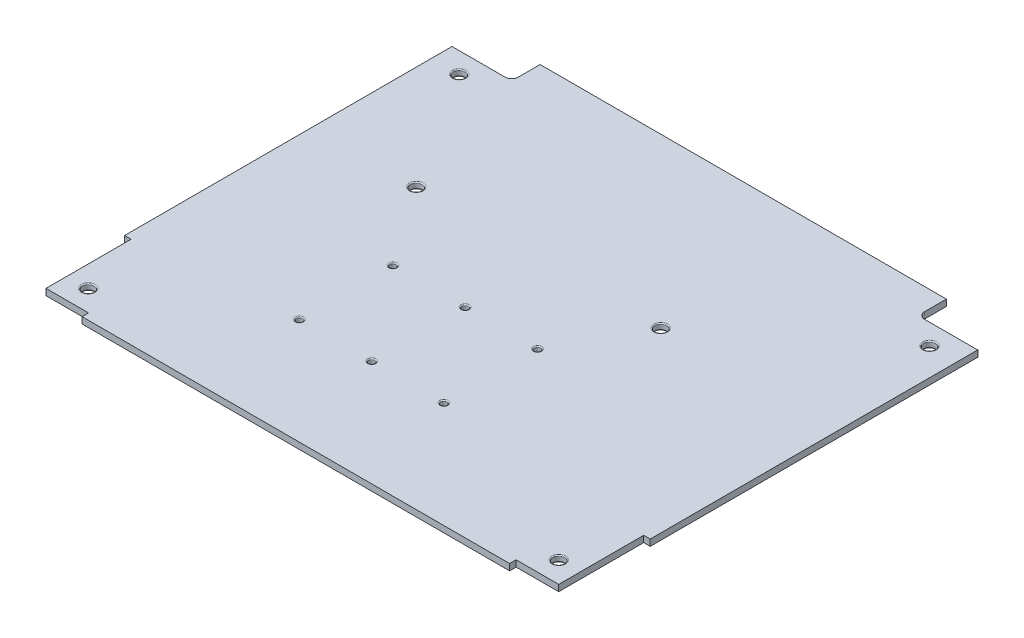
SolidWorks part; units mm, degrees
ref_plane "Front Plane" through (0, 0, 0) normal (0, 0, 1) x (1, 0, 0)
ref_plane "Top Plane" through (0, 0, 0) normal (0, 1, 0) x (1, 0, 0)
ref_plane "Right Plane" through (0, 0, 0) normal (1, 0, 0) x (0, 0, -1)
sketch "Sketch1" plane through (0, 0, 0) normal (0, 1, 0) x (1, 0, 0)
  line L1 (-123.65, -105.2375) -> (123.65, -105.2375)
  line L2 (-123.65, -105.2375) -> (-123.65, 105.2375)
  line L3 (-123.65, 105.2375) -> (123.65, 105.2375)
  line L4 (123.65, -105.2375) -> (123.65, 105.2375)
  line L5 (-123.65, -105.2375) -> (123.65, 105.2375) construction
  line L6 (-123.65, 105.2375) -> (123.65, -105.2375) construction
  point P0 (0, 0)
  dimension "D1" = 247.3
  dimension "D2" = 210.475
extrude "Boss-Extrude1" add sketch "Sketch1" along normal blind 3
sketch "Sketch4" plane through (0, 3, 0) normal (0, 1, 0) x (1, 0, 0)
  line L0 (0, 0) -> (0, -50000) construction
  line L5 (120.6, -102.1875) -> (100.6, -105.2375) construction
  line L15 (-123.65, -105.2375) -> (-120.6, -105.2375)
  line L16 (-123.65, -105.2375) -> (-123.65, -62.1875)
  line L21 (-123.65, -62.1875) -> (-120.6, -62.1875)
  line L23 (-120.6, -102.1875) -> (-120.6, -62.1875)
  line L24 (-123.65, -105.2375) -> (-120.6, -62.1875) construction
  line L25 (-123.65, -62.1875) -> (-120.6, -105.2375) construction
  line L34 (0, 0) -> (50000, 0) construction
  line L35 (-120.6, -105.2375) -> (-100.6, -105.2375)
  line L37 (-120.6, -102.1875) -> (-100.6, -102.1875)
  line L38 (-100.6, -105.2375) -> (-100.6, -102.1875)
  line L39 (-120.6, -105.2375) -> (-100.6, -102.1875) construction
  line L40 (-120.6, -102.1875) -> (-100.6, -105.2375) construction
  line L41 (120.6, -105.2375) -> (100.6, -102.1875) construction
  line L42 (123.65, -62.1875) -> (120.6, -105.2375) construction
  line L43 (123.65, -105.2375) -> (120.6, -62.1875) construction
  line L44 (100.6, -105.2375) -> (100.6, -102.1875)
  line L45 (120.6, -102.1875) -> (100.6, -102.1875)
  line L46 (120.6, -105.2375) -> (100.6, -105.2375)
  line L47 (120.6, -102.1875) -> (120.6, -62.1875)
  line L48 (123.65, -62.1875) -> (120.6, -62.1875)
  line L49 (123.65, -105.2375) -> (123.65, -62.1875)
  line L50 (123.65, -105.2375) -> (120.6, -105.2375)
  point P4 (-122.125, -83.7125)
  point P9 (-110.6, -103.7125)
  point P19 (110.6, -103.7125)
  point P20 (122.125, -83.7125)
  dimension "D1" = 43.05
  dimension "D2" = 3.05
  dimension "D3" = 3.05
  dimension "D4" = 23.05
extrude "Cut-Extrude2" cut sketch "Sketch4" against normal through all
sketch "Sketch2" plane through (0, 3, 0) normal (0, 1, 0) x (1, 0, 0)
  line L0 (0, 0) -> (50000, 0) construction
  line L1 (0, 0) -> (0, 50000) construction
  line L2 (-123.65, 105.2375) -> (-123.65, -62.1875) construction
  line L3 (123.65, 105.2375) -> (-123.65, 105.2375) construction
  line L4 (-100.6, -105.2375) -> (100.6, -105.2375) construction
  circle A0 centre (-110.65, 82.2375) radius 2.75
  circle A1 centre (110.65, 82.2375) radius 2.75
  circle A4 centre (-110.65, -92.2375) radius 2.75
  circle A5 centre (110.65, -92.2375) radius 2.75
  dimension "D1" = 5.5
  dimension "D2" = 13
  dimension "D3" = 23
  dimension "D4" = 13
extrude "Cut-Extrude1" cut sketch "Sketch2" against normal through all
fillet "Fillet1" radius 0.5 8 edges at (-110.65, 3, -79.4875) (-110.65, 0, -79.4875) (110.65, 3, -84.9875) (110.65, 0, -84.9875) (-110.65, 3, 94.9875) (-110.65, 0, 94.9875) (110.65, 3, 89.4875) (110.65, 0, 89.4875)
sketch "Sketch5" plane through (0, 3, 0) normal (0, 1, 0) x (1, 0, 0)
  line L5 (-10, 35.175) -> (10, 35.175)
  line L6 (15.05, 40.225) -> (15.05, 105.2375)
  line L8 (-15.05, 105.2375) -> (-15.05, 40.225)
  line L9 (-10, 35.225) -> (10, 35.225)
  line L10 (15, 40.225) -> (15, 92.225)
  line L11 (15, 92.225) -> (-15, 92.225)
  line L12 (-15, 92.225) -> (-15, 40.225)
  line L13 (-10, 35.225) -> (10, 35.225) construction
  line L14 (15, 40.225) -> (15, 92.225) construction
  line L15 (15, 92.225) -> (-15, 92.225) construction
  line L16 (-15, 92.225) -> (-15, 40.225) construction
  line L17 (15.05, 92.275) -> (-15.05, 92.275) construction
  line L18 (-15.05, 105.2375) -> (15.05, 105.2375)
  line L19 (123.65, 105.2375) -> (-123.65, 105.2375) construction
  line L20 (15.05, 40.225) -> (15.05, 92.275) construction
  line L21 (-15.05, 92.275) -> (-15.05, 40.225) construction
  arc A2 (10, 35.175) -> (15.05, 40.225) centre (10, 40.225) ccw
  arc A3 (-15.05, 40.225) -> (-10, 35.175) centre (-10, 40.225) ccw
  arc A4 (10, 35.225) -> (15, 40.225) centre (10, 40.225) ccw
  arc A5 (-15, 40.225) -> (-10, 35.225) centre (-10, 40.225) ccw
  arc A6 (10, 35.225) -> (15, 40.225) centre (10, 40.225) ccw construction
  arc A7 (-15, 40.225) -> (-10, 35.225) centre (-10, 40.225) ccw construction
  dimension "D1" = 0
  dimension "D2" = 0.05
extrude "Cut-Extrude3" [suppressed] cut sketch "Sketch5" against normal through all
sketch "Sketch6" plane through (0, 3, 0) normal (0, 1, 0) x (1, 0, 0)
  line L0 (-123.65, 105.2375) -> (-123.65, -62.1875) construction
  line L1 (-123.65, -72.4875) -> (-98.57, -72.4875)
  line L2 (-123.65, -72.4875) -> (-123.65, -8.8875)
  line L3 (-123.65, -8.8875) -> (-98.57, -8.8875)
  line L4 (-95.57, -69.4875) -> (-95.57, -11.8875)
  line L5 (-100.6, -105.2375) -> (100.6, -105.2375) construction
  line L6 (0, 0) -> (0, -50000) construction
  line L7 (95.57, -69.4875) -> (95.57, -11.8875)
  line L8 (123.65, -8.8875) -> (98.57, -8.8875)
  line L9 (123.65, -72.4875) -> (123.65, -8.8875)
  line L10 (123.65, -72.4875) -> (98.57, -72.4875)
  arc A0 (98.57, -72.4875) -> (95.57, -69.4875) centre (98.57, -69.4875) cw
  arc A1 (95.57, -11.8875) -> (98.57, -8.8875) centre (98.57, -11.8875) cw
  arc A2 (-98.57, -72.4875) -> (-95.57, -69.4875) centre (-98.57, -69.4875) ccw
  arc A3 (-95.57, -11.8875) -> (-98.57, -8.8875) centre (-98.57, -11.8875) ccw
  point P17 (95.57, -72.4875)
  point P20 (95.57, -8.8875)
  point P23 (-95.57, -72.4875)
  point P26 (-95.57, -8.8875)
  dimension "D4" = 3
  dimension "D1" = 32.75
  dimension "D2" = 63.6
  dimension "D3" = 28.08
extrude "Cut-Extrude4" [suppressed] cut sketch "Sketch6" against normal through all
sketch "Sketch8" plane through (0, 3, 0) normal (0, 1, 0) x (1, 0, 0)
  line L0 (-14.35, -33.2375) -> (-14.35, 49966.7625) construction
  line L1 (53.65, -55.2375) -> (-82.35, -55.2375) construction
  line L2 (53.65, -55.2375) -> (53.65, -11.2375) construction
  line L3 (53.65, -11.2375) -> (-82.35, -11.2375) construction
  line L4 (-82.35, -55.2375) -> (-82.35, -11.2375) construction
  line L5 (53.65, -55.2375) -> (-82.35, -11.2375) construction
  line L6 (53.65, -11.2375) -> (-82.35, -55.2375) construction
  line L7 (-14.35, -33.2375) -> (-50014.35, -33.2375) construction
  circle A0 centre (19.65, -55.2375) radius 1.5
  circle A1 centre (-14.35, -55.2375) radius 1.5
  circle A2 centre (-48.35, -55.2375) radius 1.5
  circle A3 centre (-48.35, -11.2375) radius 1.5
  circle A4 centre (-14.35, -11.2375) radius 1.5
  circle A5 centre (19.65, -11.2375) radius 1.5
  point P4 (-14.35, -33.2375)
  dimension "D1" = 3
  dimension "D3" = 34
extrude "Cut-Extrude6" cut sketch "Sketch8" against normal through all
fillet "Fillet2" radius 0.5 12 edges at (19.65, 3, 56.7375) (19.65, 0, 56.7375) (-14.35, 3, 56.7375) (-14.35, 0, 56.7375) (-48.35, 3, 53.7375) (-48.35, 0, 53.7375) (-48.35, 3, 12.7375) (-48.35, 0, 12.7375) (-14.35, 3, 9.7375) (-14.35, 0, 9.7375) (19.65, 3, 9.7375) (19.65, 0, 9.7375)
sketch "Sketch9" plane through (0, 3, 0) normal (0, 1, 0) x (1, 0, 0)
  circle A2 centre (-74.85, 26.2625) radius 2.75 construction
  circle A5 centre (40.15, 26.2625) radius 2.75 construction
  circle A8 centre (-74.85, 26.2625) radius 2.75
  circle A11 centre (40.15, 26.2625) radius 2.75
extrude "Cut-Extrude7" cut sketch "Sketch9" against normal through all
fillet "Fillet3" radius 0.5 4 edges at (-74.85, 3, -23.5125) (-74.85, 0, -23.5125) (40.15, 3, -23.5125) (40.15, 0, -23.5125)
sketch "Sketch10" [suppressed] plane through (0, 3, 0) normal (0, 1, 0) x (1, 0, 0)
  circle A0 centre (74.85, 49.2625) radius 2.75 construction
  circle A1 centre (-40.15, 49.2625) radius 2.75 construction
  circle A2 centre (74.85, 49.2625) radius 2.75
  circle A3 centre (-40.15, 49.2625) radius 2.75
extrude "Cut-Extrude8" [suppressed] cut sketch "Sketch10" against normal through all
fillet "Fillet4" [suppressed] radius 0.5
sketch "Sketch11" [suppressed] plane through (0, 3, 0) normal (0, 1, 0) x (1, 0, 0)
  line L0 (-123.65, 43.775) -> (-123.65, -0.725) construction
  line L1 (-83.65, 14.225) -> (-33.65, 14.225)
  line L6 (-83.65, 14.225) -> (-83.65, -35.775)
  line L8 (-83.65, -35.775) -> (-33.65, -35.775)
  line L9 (-33.65, 14.225) -> (-33.65, -35.775)
  line L10 (-83.65, 14.225) -> (-33.65, -35.775) construction
  line L11 (-83.65, -35.775) -> (-33.65, 14.225) construction
  circle A8 centre (-78.65, -30.775) radius 2.75
  circle A9 centre (-110.65, -30.775) radius 2.75 construction
  circle A10 centre (-110.65, -30.775) radius 2.75 construction
  circle A11 centre (-78.65, 9.225) radius 2.75
  circle A12 centre (-38.65, 9.225) radius 2.75
  circle A13 centre (-38.65, -30.775) radius 2.75
  point P4 (-58.65, -10.775)
  point P21 (-58.65, -10.775)
  dimension "D3" = 5
  dimension "D4" = 5.5
  dimension "D1" = 50
  dimension "D2" = 40
  dimension "D5" = 4
extrude "Cut-Extrude9" [suppressed] cut sketch "Sketch11" against normal through all contours A11 | A8 | A13 | A12
fillet "Fillet5" [suppressed] radius 0.5
sketch "Sketch12" plane through (0, 0, 0) normal (0, -1, 0) x (1, 0, 0)
  line L0 (0, 0) -> (0, 50000) construction
  line L4 (98.625, -155.4145) -> (122.675, -155.4145)
  line L5 (125.675, -152.4145) -> (125.675, -94.9145)
  line L6 (122.675, -91.9145) -> (98.625, -91.9145)
  line L7 (95.625, -94.9145) -> (95.625, -152.4145)
  line L9 (125.675, -105.2375) -> (125.675, -94.9145) construction
  line L10 (122.675, -91.9145) -> (98.625, -91.9145) construction
  line L11 (95.625, -94.9145) -> (95.625, -105.2375) construction
  line L12 (123.65, -105.2375) -> (-123.65, -105.2375) construction
  line L13 (123.65, -105.2375) -> (-123.65, -105.2375) construction
  line L15 (125.725, -105.2375) -> (125.725, -94.9145)
  line L16 (122.675, -91.8645) -> (98.625, -91.8645)
  line L17 (95.575, -94.9145) -> (95.575, -105.2375)
  line L18 (95.625, -105.2375) -> (125.675, -105.2375) construction
  line L19 (95.575, -105.2875) -> (125.725, -105.2875) construction
  line L20 (95.575, -105.2375) -> (125.725, -105.2375)
  line L21 (125.725, -105.2875) -> (125.725, -94.9145) construction
  line L22 (95.575, -94.9145) -> (95.575, -105.2875) construction
  line L23 (95.625, -152.4145) -> (95.625, -94.9145) construction
  line L24 (-95.625, -94.9145) -> (-95.625, -105.2375) construction
  line L25 (-122.675, -91.9145) -> (-98.625, -91.9145) construction
  line L26 (-125.675, -105.2375) -> (-125.675, -94.9145) construction
  line L27 (-95.575, -105.2375) -> (-125.725, -105.2375)
  line L28 (-95.575, -94.9145) -> (-95.575, -105.2375)
  line L29 (-122.675, -91.8645) -> (-98.625, -91.8645)
  line L30 (-125.725, -105.2375) -> (-125.725, -94.9145)
  arc A0 (125.725, -94.9145) -> (122.675, -91.8645) centre (122.675, -94.9145) ccw
  arc A1 (98.625, -91.8645) -> (95.575, -94.9145) centre (98.625, -94.9145) ccw
  arc A2 (-98.625, -91.9145) -> (-95.625, -94.9145) centre (-98.625, -94.9145) cw construction
  arc A3 (-125.675, -94.9145) -> (-122.675, -91.9145) centre (-122.675, -94.9145) cw construction
  arc A4 (122.675, -155.4145) -> (125.675, -152.4145) centre (122.675, -152.4145) ccw
  arc A5 (125.675, -94.9145) -> (122.675, -91.9145) centre (122.675, -94.9145) ccw
  arc A6 (98.625, -91.9145) -> (95.625, -94.9145) centre (98.625, -94.9145) ccw
  arc A7 (95.625, -152.4145) -> (98.625, -155.4145) centre (98.625, -152.4145) ccw
  arc A9 (125.675, -94.9145) -> (122.675, -91.9145) centre (122.675, -94.9145) ccw construction
  arc A10 (98.625, -91.9145) -> (95.625, -94.9145) centre (98.625, -94.9145) ccw construction
  arc A12 (-98.625, -91.8645) -> (-95.575, -94.9145) centre (-98.625, -94.9145) cw
  arc A13 (-125.725, -94.9145) -> (-122.675, -91.8645) centre (-122.675, -94.9145) cw
  dimension "D1" = 0
  dimension "D2" = 0.05
extrude "Cut-Extrude10" cut sketch "Sketch12" against normal through all
sketch "Sketch13" [suppressed] plane through (0, 0, 0) normal (0, -1, 0) x (1, 0, 0)
  line L0 (122.675, -35.1105) -> (98.625, -35.1105) construction
  line L1 (95.625, -38.1105) -> (95.625, -95.6105) construction
  line L2 (98.625, -98.6105) -> (122.675, -98.6105) construction
  line L3 (125.675, -95.6105) -> (125.675, -38.1105) construction
  line L4 (-98.625, -35.1105) -> (-122.675, -35.1105) construction
  line L5 (-125.675, -38.1105) -> (-125.675, -95.6105) construction
  line L6 (-122.675, -98.6105) -> (-98.625, -98.6105) construction
  line L7 (-95.625, -95.6105) -> (-95.625, -38.1105) construction
  line L8 (122.675, -35.1105) -> (98.625, -35.1105) construction
  line L9 (95.625, -38.1105) -> (95.625, -95.6105) construction
  line L10 (98.625, -98.6105) -> (122.675, -98.6105) construction
  line L11 (125.675, -95.6105) -> (125.675, -38.1105) construction
  line L12 (-98.625, -35.1105) -> (-122.675, -35.1105) construction
  line L13 (-125.675, -38.1105) -> (-125.675, -95.6105) construction
  line L14 (-122.675, -98.6105) -> (-98.625, -98.6105) construction
  line L15 (-95.625, -95.6105) -> (-95.625, -38.1105) construction
  line L16 (122.675, -35.0605) -> (98.625, -35.0605)
  line L17 (95.575, -38.1105) -> (95.575, -95.6105)
  line L18 (98.625, -98.6605) -> (122.675, -98.6605)
  line L19 (125.725, -95.6105) -> (125.725, -38.1105)
  line L20 (-98.625, -35.0605) -> (-122.675, -35.0605)
  line L21 (-125.725, -38.1105) -> (-125.725, -95.6105)
  line L22 (-122.675, -98.6605) -> (-98.625, -98.6605)
  line L23 (-95.575, -95.6105) -> (-95.575, -38.1105)
  arc A0 (98.625, -35.1105) -> (95.625, -38.1105) centre (98.625, -38.1105) ccw construction
  arc A1 (95.625, -95.6105) -> (98.625, -98.6105) centre (98.625, -95.6105) ccw construction
  arc A2 (122.675, -98.6105) -> (125.675, -95.6105) centre (122.675, -95.6105) ccw construction
  arc A3 (125.675, -38.1105) -> (122.675, -35.1105) centre (122.675, -38.1105) ccw construction
  arc A4 (-122.675, -35.1105) -> (-125.675, -38.1105) centre (-122.675, -38.1105) ccw construction
  arc A5 (-125.675, -95.6105) -> (-122.675, -98.6105) centre (-122.675, -95.6105) ccw construction
  arc A6 (-98.625, -98.6105) -> (-95.625, -95.6105) centre (-98.625, -95.6105) ccw construction
  arc A7 (-95.625, -38.1105) -> (-98.625, -35.1105) centre (-98.625, -38.1105) ccw construction
  arc A8 (98.625, -35.1105) -> (95.625, -38.1105) centre (98.625, -38.1105) ccw construction
  arc A9 (95.625, -95.6105) -> (98.625, -98.6105) centre (98.625, -95.6105) ccw construction
  arc A10 (122.675, -98.6105) -> (125.675, -95.6105) centre (122.675, -95.6105) ccw construction
  arc A11 (125.675, -38.1105) -> (122.675, -35.1105) centre (122.675, -38.1105) ccw construction
  arc A12 (-122.675, -35.1105) -> (-125.675, -38.1105) centre (-122.675, -38.1105) ccw construction
  arc A13 (-125.675, -95.6105) -> (-122.675, -98.6105) centre (-122.675, -95.6105) ccw construction
  arc A14 (-98.625, -98.6105) -> (-95.625, -95.6105) centre (-98.625, -95.6105) ccw construction
  arc A15 (-95.625, -38.1105) -> (-98.625, -35.1105) centre (-98.625, -38.1105) ccw construction
  arc A16 (98.625, -35.0605) -> (95.575, -38.1105) centre (98.625, -38.1105) ccw
  arc A17 (95.575, -95.6105) -> (98.625, -98.6605) centre (98.625, -95.6105) ccw
  arc A18 (122.675, -98.6605) -> (125.725, -95.6105) centre (122.675, -95.6105) ccw
  arc A19 (125.725, -38.1105) -> (122.675, -35.0605) centre (122.675, -38.1105) ccw
  arc A20 (-122.675, -35.0605) -> (-125.725, -38.1105) centre (-122.675, -38.1105) ccw
  arc A21 (-125.725, -95.6105) -> (-122.675, -98.6605) centre (-122.675, -95.6105) ccw
  arc A22 (-98.625, -98.6605) -> (-95.575, -95.6105) centre (-98.625, -95.6105) ccw
  arc A23 (-95.575, -38.1105) -> (-98.625, -35.0605) centre (-98.625, -38.1105) ccw
  dimension "D1" = 0.05
extrude "Cut-Extrude11" [suppressed] cut sketch "Sketch13" against normal through all
sketch "Sketch14" [suppressed] plane through (0, 3, 0) normal (0, 1, 0) x (1, 0, 0)
  line L0 (-123.65, 35.2205) -> (-123.65, -42.1875) construction
  line L1 (-96.15, 11.5165) -> (-91.15, 11.5165) construction
  line L2 (-101.15, 6.5165) -> (-101.15, -13.4835) construction
  line L3 (-96.15, -18.4835) -> (-91.15, -18.4835) construction
  line L4 (-86.15, 6.5165) -> (-86.15, -13.4835) construction
  line L5 (-101.15, 11.5165) -> (-86.15, -18.4835) construction
  line L6 (-101.15, -18.4835) -> (-86.15, 11.5165) construction
  line L7 (0, -1.65) -> (0, 1.65) construction
  line L8 (101.15, -18.4835) -> (86.15, 11.5165) construction
  line L9 (101.15, 11.5165) -> (86.15, -18.4835) construction
  line L10 (86.15, 6.5165) -> (86.15, -13.4835) construction
  line L11 (96.15, -18.4835) -> (91.15, -18.4835) construction
  line L12 (101.15, 6.5165) -> (101.15, -13.4835) construction
  line L13 (96.15, 11.5165) -> (91.15, 11.5165) construction
  arc A0 (-101.15, -13.4835) -> (-96.15, -18.4835) centre (-96.15, -13.4835) ccw construction
  arc A1 (-91.15, -18.4835) -> (-86.15, -13.4835) centre (-91.15, -13.4835) ccw construction
  arc A2 (-86.15, 6.5165) -> (-91.15, 11.5165) centre (-91.15, 6.5165) ccw construction
  arc A3 (-96.15, 11.5165) -> (-101.15, 6.5165) centre (-96.15, 6.5165) ccw construction
  arc A4 (96.15, 11.5165) -> (101.15, 6.5165) centre (96.15, 6.5165) cw construction
  arc A5 (86.15, 6.5165) -> (91.15, 11.5165) centre (91.15, 6.5165) cw construction
  arc A6 (91.15, -18.4835) -> (86.15, -13.4835) centre (91.15, -13.4835) cw construction
  arc A7 (101.15, -13.4835) -> (96.15, -18.4835) centre (96.15, -13.4835) cw construction
  circle A8 centre (-93.65, -3.4835) radius 8.255
  circle A10 centre (93.65, -3.4835) radius 8.255
  point P4 (-93.65, -3.4835)
  point P7 (-123.65, -3.4835)
  point P38 (123.65, -3.4835)
  point P39 (93.65, -3.4835)
  dimension "D4" = 5
  dimension "D5" = 16.51
  dimension "D1" = 30
  dimension "D2" = 15
  dimension "D3" = 30
extrude "Cut-Extrude12" [suppressed] cut sketch "Sketch14" against normal through all
